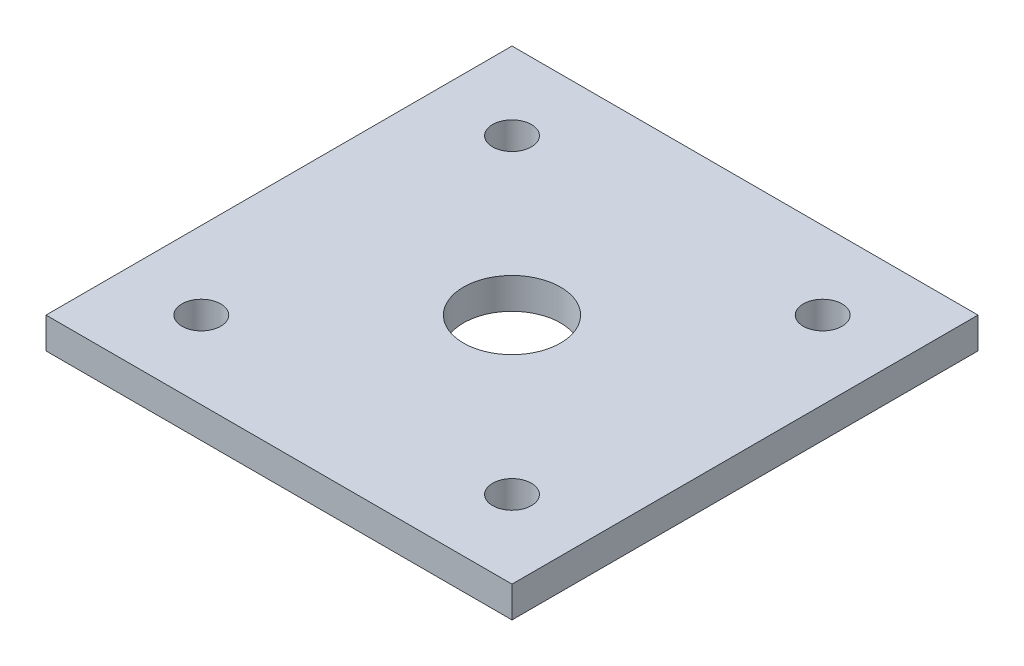
SolidWorks part; units mm, degrees
ref_plane "Front Plane" through (0, 0, 0) normal (0, 0, 1) x (1, 0, 0)
ref_plane "Top Plane" through (0, 0, 0) normal (0, 1, 0) x (1, 0, 0)
ref_plane "Right Plane" through (0, 0, 0) normal (1, 0, 0) x (0, 0, -1)
sketch "Sketch1" plane through (0, 0, 0) normal (0, 1, 0) x (1, 0, 0)
  line L1 (-60, 60) -> (60, 60)
  line L2 (-60, 60) -> (-60, -60)
  line L3 (-60, -60) -> (60, -60)
  line L4 (60, 60) -> (60, -60)
  line L5 (-60, 60) -> (60, -60) construction
  line L6 (-60, -60) -> (60, 60) construction
  point P1 (0, 0)
  dimension "D1" = 120
extrude "Boss-Extrude2" add sketch "Sketch1" along normal blind 8
sketch "Sketch3" plane through (0, 8, 0) normal (0, 1, 0) x (1, 0, 0)
  circle A0 centre (0, 0) radius 12.5
  dimension "D1" = 25
extrude "Cut-Extrude1" cut sketch "Sketch3" against normal through all
sketch "Sketch4" plane through (0, 8, 0) normal (0, 1, 0) x (1, 0, 0)
  circle A0 centre (-40, 40) radius 5
  circle A1 centre (40, 40) radius 5
  circle A2 centre (40, -40) radius 5
  circle A3 centre (-40, -40) radius 5
  dimension "D1" = 10
  dimension "D2" = 20
  dimension "D3" = 20
  dimension "D4" = 2
  dimension "D5" = 2
extrude "Cut-Extrude2" cut sketch "Sketch4" against normal blind 10
